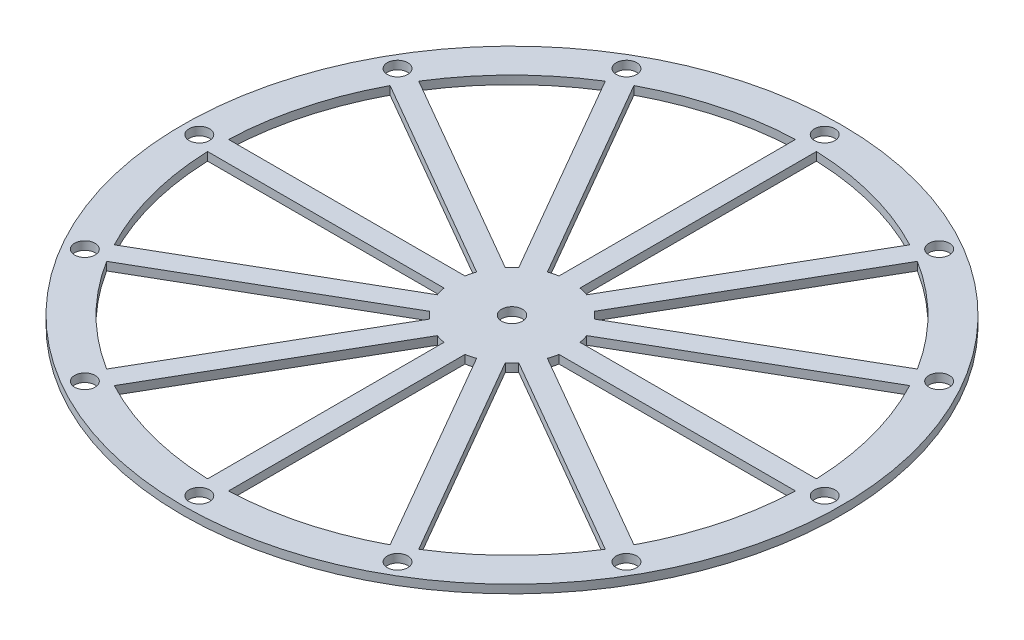
SolidWorks part; units mm, degrees
ref_plane "Front Plane" through (0, 0, 0) normal (0, 0, 1) x (1, 0, 0)
ref_plane "Top Plane" through (0, 0, 0) normal (0, 1, 0) x (1, 0, 0)
ref_plane "Right Plane" through (0, 0, 0) normal (1, 0, 0) x (0, 0, -1)
sketch "Sketch1" plane through (0, 0, 0) normal (0, 1, 0) x (1, 0, 0)
  line L0 (0, 566.1108) -> (0, -589.7934) construction
  line L1 (15.084, 423.1822) -> (15.084, 82.7828)
  line L2 (-15.084, 423.1822) -> (-15.084, 82.7828)
  line L3 (224.6542, 358.9445) -> (54.4545, 64.15)
  line L4 (198.5279, 374.0285) -> (28.3282, 79.234)
  line L5 (374.0285, 198.5279) -> (79.234, 28.3282)
  line L6 (358.9445, 224.6542) -> (64.15, 54.4545)
  line L7 (423.1822, -15.084) -> (82.7828, -15.084)
  line L8 (423.1822, 15.084) -> (82.7828, 15.084)
  line L9 (358.9445, -224.6542) -> (64.15, -54.4545)
  line L10 (374.0285, -198.5279) -> (79.234, -28.3282)
  line L11 (198.5279, -374.0285) -> (28.3282, -79.234)
  line L12 (224.6542, -358.9445) -> (54.4545, -64.15)
  line L13 (-15.084, -423.1822) -> (-15.084, -82.7828)
  line L14 (15.084, -423.1822) -> (15.084, -82.7828)
  line L15 (-224.6542, -358.9445) -> (-54.4545, -64.15)
  line L16 (-198.5279, -374.0285) -> (-28.3282, -79.234)
  line L17 (-374.0285, -198.5279) -> (-79.234, -28.3282)
  line L18 (-358.9445, -224.6542) -> (-64.15, -54.4545)
  line L19 (-423.1822, 15.084) -> (-82.7828, 15.084)
  line L20 (-423.1822, -15.084) -> (-82.7828, -15.084)
  line L21 (-358.9445, 224.6542) -> (-64.15, 54.4545)
  line L22 (-374.0285, 198.5279) -> (-79.234, 28.3282)
  line L23 (-198.5279, 374.0285) -> (-28.3282, 79.234)
  line L24 (-224.6542, 358.9445) -> (-54.4545, 64.15)
  circle A0 centre (0, 0) radius 474.4323
  circle A1 centre (0, 0) radius 15
  arc A2 (-224.6542, 358.9445) -> (-358.9445, 224.6542) centre (0, 0) ccw
  arc A3 (-82.7828, -15.084) -> (-79.234, -28.3282) centre (0, 0) ccw
  arc A4 (-374.0285, 198.5279) -> (-423.1822, 15.084) centre (0, 0) ccw
  arc A5 (-423.1822, -15.084) -> (-374.0285, -198.5279) centre (0, 0) ccw
  arc A6 (-79.234, 28.3282) -> (-82.7828, 15.084) centre (0, 0) ccw
  arc A7 (-54.4545, 64.15) -> (-64.15, 54.4545) centre (0, 0) ccw
  arc A8 (28.3282, 79.234) -> (15.084, 82.7828) centre (0, 0) ccw
  arc A9 (64.15, 54.4545) -> (54.4545, 64.15) centre (0, 0) ccw
  arc A10 (82.7828, 15.084) -> (79.234, 28.3282) centre (0, 0) ccw
  arc A11 (79.234, -28.3282) -> (82.7828, -15.084) centre (0, 0) ccw
  arc A12 (54.4545, -64.15) -> (64.15, -54.4545) centre (0, 0) ccw
  arc A13 (-64.15, -54.4545) -> (-54.4545, -64.15) centre (0, 0) ccw
  arc A14 (-28.3282, -79.234) -> (-15.084, -82.7828) centre (0, 0) ccw
  arc A15 (423.1822, 15.084) -> (374.0285, 198.5279) centre (0, 0) ccw
  arc A16 (358.9445, 224.6542) -> (224.6542, 358.9445) centre (0, 0) ccw
  arc A17 (198.5279, 374.0285) -> (15.084, 423.1822) centre (0, 0) ccw
  arc A18 (374.0285, -198.5279) -> (423.1822, -15.084) centre (0, 0) ccw
  arc A19 (-358.9445, -224.6542) -> (-224.6542, -358.9445) centre (0, 0) ccw
  arc A20 (-198.5279, -374.0285) -> (-15.084, -423.1822) centre (0, 0) ccw
  arc A21 (15.084, -423.1822) -> (198.5279, -374.0285) centre (0, 0) ccw
  arc A22 (15.084, -82.7828) -> (28.3282, -79.234) centre (0, 0) ccw
  arc A23 (224.6542, -358.9445) -> (358.9445, -224.6542) centre (0, 0) ccw
  arc A24 (-15.084, 82.7828) -> (-28.3282, 79.234) centre (0, 0) ccw
  arc A25 (-15.084, 423.1822) -> (-198.5279, 374.0285) centre (0, 0) ccw
  circle A26 centre (0, 450.1688) radius 14.7383
  circle A27 centre (225.0844, 389.8576) radius 14.7383
  circle A28 centre (389.8576, 225.0844) radius 14.7383
  circle A29 centre (450.1688, 0) radius 14.7383
  circle A30 centre (389.8576, -225.0844) radius 14.7383
  circle A31 centre (225.0844, -389.8576) radius 14.7383
  circle A32 centre (0, -450.1688) radius 14.7383
  circle A33 centre (-225.0844, -389.8576) radius 14.7383
  circle A34 centre (-389.8576, -225.0844) radius 14.7383
  circle A35 centre (-450.1688, 0) radius 14.7383
  circle A36 centre (-389.8576, 225.0844) radius 14.7383
  circle A37 centre (-225.0844, 389.8576) radius 14.7383
  point P58 (0, 0)
  point P82 (0, 0)
  dimension "D1" = 12
  dimension "D2" = 12
extrude "Boss-Extrude15" add sketch "Sketch1" along normal blind 12
